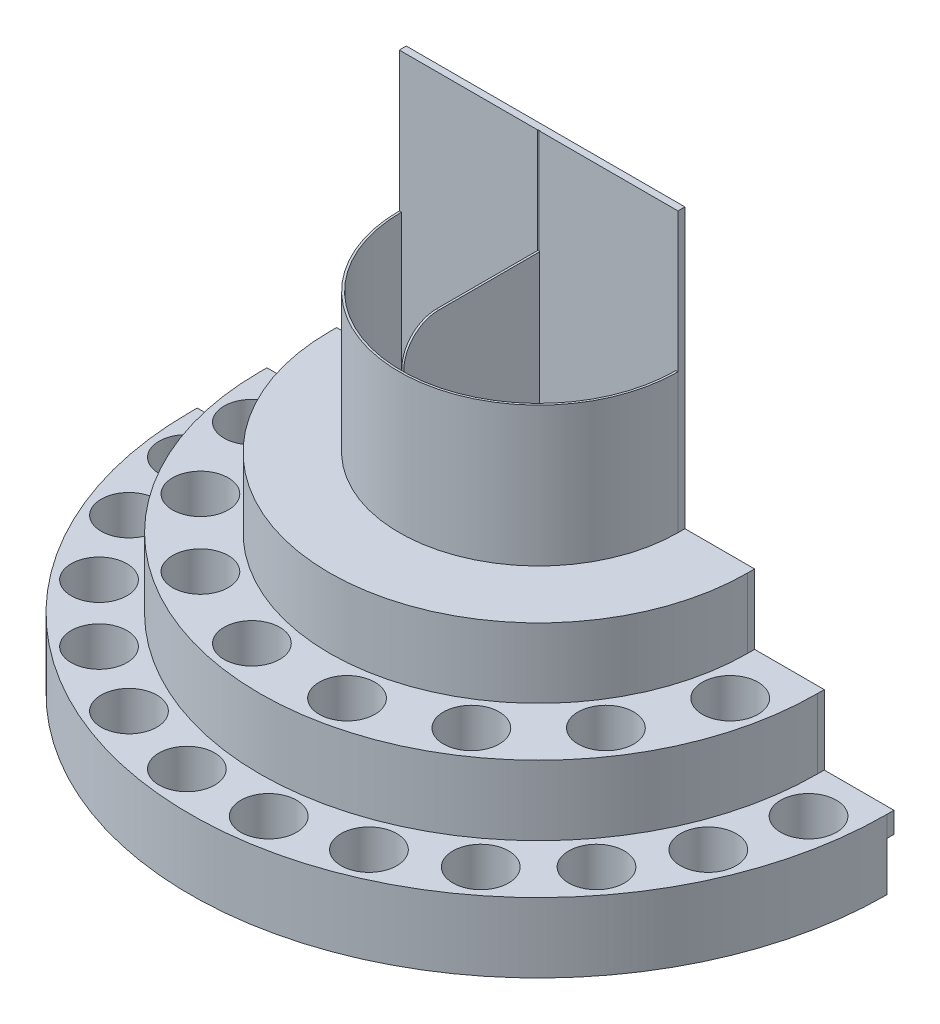
SolidWorks part; units mm, degrees
ref_plane "Plan de face" through (0, 0, 0) normal (0, 0, 1) x (1, 0, 0)
ref_plane "Plan de dessus" through (0, 0, 0) normal (0, 1, 0) x (1, 0, 0)
ref_plane "Plan de droite" through (0, 0, 0) normal (1, 0, 0) x (0, 0, -1)
sketch "Esquisse1" plane through (0, 0, 0) normal (0, 1, 0) x (1, 0, 0)
  line L0 (-500, 0) -> (0, 0)
  line L1 (500, 0) -> (0, 0)
  arc A0 (-500, 0) -> (500, 0) centre (0, 0) ccw
  dimension "D1" = 500
extrude "Extrusion1" add sketch "Esquisse1" along normal blind 100
sketch "Esquisse2" plane through (0, 100, 0) normal (0, 1, 0) x (-1, 0, 0)
  line L0 (-500, 0) -> (500, 0) construction
  line L1 (400, 0) -> (-400, 0)
  arc A0 (400, 0) -> (-400, 0) centre (0, 0) ccw
  dimension "D1" = 400
extrude "Extrusion2" add sketch "Esquisse2" along normal blind 100
sketch "Esquisse3" plane through (0, 200, 0) normal (0, 1, 0) x (-1, 0, 0)
  line L0 (-400, 0) -> (400, 0) construction
  line L1 (300, 0) -> (-300, 0)
  arc A0 (300, 0) -> (-300, 0) centre (0, 0) ccw
  dimension "D1" = 300
extrude "Extrusion3" add sketch "Esquisse3" along normal blind 100
sketch "Esquisse4" plane through (0, 300, 0) normal (0, 1, 0) x (-1, 0, 0)
  line L0 (-300, 0) -> (300, 0) construction
  line L1 (200, 0) -> (197, 0)
  line L2 (-197, 0) -> (-200, 0)
  arc A0 (197, 0) -> (-197, 0) centre (0, 0) ccw
  arc A1 (200, 0) -> (-200, 0) centre (0, 0) ccw
  dimension "D1" = 3
  dimension "D2" = 200
extrude "Extrusion4" add sketch "Esquisse4" along normal blind 200
sketch "Esquisse5" plane through (0, 0, 0) normal (0, 0, -1) x (-1, 0, 0)
  line L0 (0, 0) -> (0, 700) construction
  line L1 (200, 700) -> (-200, 700)
  line L2 (-200, 700) -> (-200, 300)
  line L3 (-300, 300) -> (-200, 300) construction
  line L4 (-200, 300) -> (-300, 300)
  line L5 (-300, 300) -> (-300, 200)
  line L6 (-300, 200) -> (-400, 200)
  line L7 (-400, 200) -> (-400, 100)
  line L8 (-400, 100) -> (-500, 100)
  line L9 (-500, 100) -> (-500, 70)
  line L11 (-500, 70) -> (-305.9412, 70)
  line L12 (-200, 500) -> (-200, 300) construction
  line L13 (-500, 0) -> (500, 0) construction
  line L14 (500, 70) -> (305.9412, 70)
  line L15 (500, 100) -> (500, 70)
  line L16 (400, 100) -> (500, 100)
  line L17 (400, 200) -> (400, 100)
  line L18 (300, 200) -> (400, 200)
  line L19 (300, 300) -> (300, 200)
  line L20 (200, 300) -> (300, 300)
  line L21 (200, 700) -> (200, 300)
  arc A0 (-305.9412, 70) -> (305.9412, 70) centre (0, -100) cw
  point P33 (0, 250)
  dimension "D2" = 350
  dimension "D1" = 700
  dimension "D3" = 70
  dimension "D4" = 180
extrude "Extrusion5" add sketch "Esquisse5" along normal blind 10
sketch "Esquisse6" plane through (0, 300, 0) normal (0, 1, 0) x (1, 0, 0)
  line L0 (0, 0) -> (-450, 0) construction
  line L1 (0, 0) -> (450, 0) construction
  line L2 (0, 0) -> (-446.1502, -58.7368) construction
  line L3 (446.1502, -58.7368) -> (0, 0) construction
  line L4 (0, 0) -> (-343.2748, -68.2816) construction
  line L5 (343.2748, -68.2816) -> (0, 0) construction
  circle A0 centre (-343.2748, -68.2816) radius 40
  circle A1 centre (-291.0144, -194.4496) radius 40
  arc A2 (-450, 0) -> (450, 0) centre (0, 0) ccw construction
  arc A3 (-350, 0) -> (350, 0) centre (0, 0) ccw construction
  arc A4 (-250, 0) -> (250, 0) centre (0, 0) ccw construction
  circle A5 centre (-446.1502, -58.7368) radius 40
  circle A6 centre (-415.7458, -172.2075) radius 40
  circle A7 centre (-357.009, -273.9426) radius 40
  circle A8 centre (-273.9426, -357.009) radius 40
  circle A9 centre (-172.2075, -415.7458) radius 40
  circle A10 centre (-58.7368, -446.1502) radius 40
  circle A11 centre (58.7368, -446.1502) radius 40
  circle A12 centre (172.2075, -415.7458) radius 40
  circle A13 centre (273.9426, -357.009) radius 40
  circle A14 centre (357.009, -273.9426) radius 40
  circle A15 centre (415.7458, -172.2075) radius 40
  circle A16 centre (446.1502, -58.7368) radius 40
  circle A17 centre (-194.4496, -291.0144) radius 40
  circle A18 centre (-68.2816, -343.2748) radius 40
  circle A19 centre (68.2816, -343.2748) radius 40
  circle A20 centre (194.4496, -291.0144) radius 40
  circle A21 centre (291.0144, -194.4496) radius 40
  circle A22 centre (343.2748, -68.2816) radius 40
  dimension "D1" = 450
  dimension "D2" = 350
  dimension "D3" = 250
  dimension "D5" = 80
  dimension "D7" = 80
  dimension "D4" = 7.5
  dimension "D6" = 7.5
  dimension "D8" = 11.25
  dimension "D9" = 11.25
extrude "Extrusion6" cut sketch "Esquisse6" against normal up to surface (300 mm away) up to face at (0, 0, 250)
sketch "Esquisse7" plane through (0, 300, 0) normal (0, 1, 0) x (1, 0, 0)
  line L0 (0, 0) -> (0, -197) construction
  line L1 (-1.5, 0) -> (1.5, 0)
  line L2 (197, 0) -> (-197, 0) construction
  line L3 (-200, 0) -> (200, 0) construction
  line L4 (-1.5, 0) -> (-1.5, -195)
  line L5 (-1.5, -195) -> (1.5, -195)
  line L6 (1.5, -195) -> (1.5, 0)
  arc A0 (-197, 0) -> (197, 0) centre (0, 0) ccw construction
  point P12 (0, 0)
  dimension "D1" = 3
  dimension "D2" = 195
extrude "Extrusion8" add sketch "Esquisse7" along normal blind 250
fillet "Congé1" radius 50 1 edges at (0, 550, 195)
sketch "Esquisse8" plane through (0, 0, 0) normal (0, 0, 1) x (1, 0, 0)
  line L0 (-1.5, 550) -> (1.5, 550)
  line L1 (1.5, 550) -> (-1.5, 550) construction
  line L2 (1.5, 550) -> (1.5, 700)
  line L3 (-200, 700) -> (200, 700) construction
  line L4 (1.5, 700) -> (-1.5, 700)
  line L5 (-1.5, 700) -> (-1.5, 550)
  line L6 (-1.5, 700) -> (-1.7348, 700.0262)
extrude "Extrusion9" cut sketch "Esquisse8" against normal blind 0.5 contours L5 L0 L2 L4
